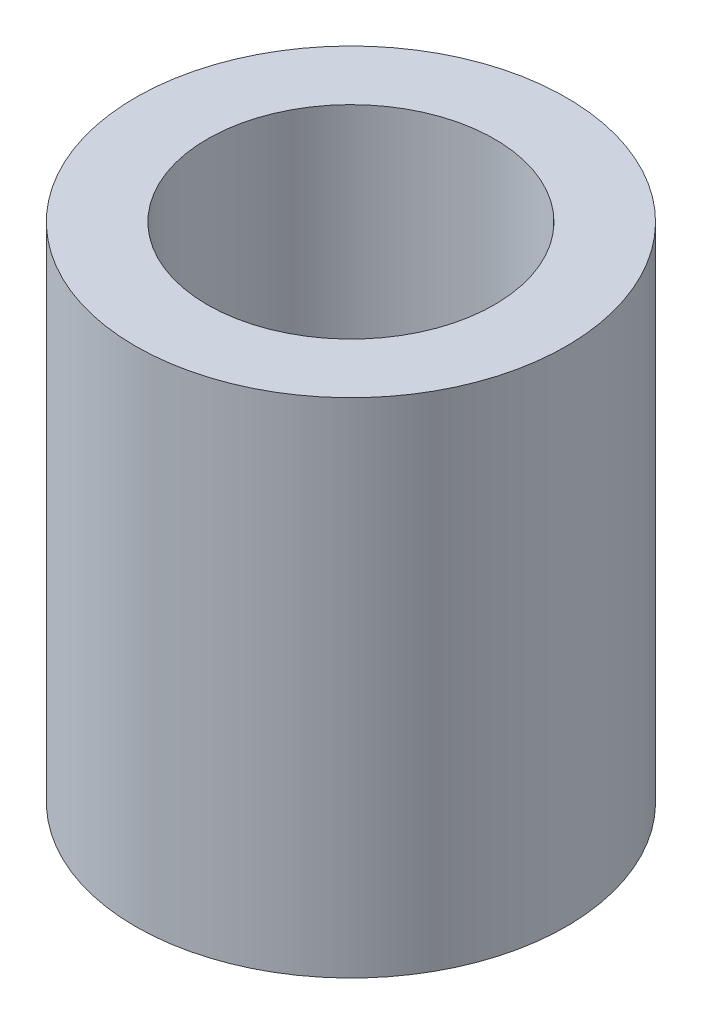
SolidWorks part; units mm, degrees
material "Латунь"
ref_plane "Спереди" through (0, 0, 0) normal (0, 0, 1) x (1, 0, 0)
ref_plane "Сверху" through (0, 0, 0) normal (0, 1, 0) x (1, 0, 0)
ref_plane "Справа" through (0, 0, 0) normal (1, 0, 0) x (0, 0, -1)
sketch "Эскиз1" plane through (0, 0, 0) normal (0, 1, 0) x (1, 0, 0)
  circle A0 centre (0, 0) radius 3
  circle A1 centre (0, 0) radius 2
  dimension "D1" = 6
  dimension "D2" = 4
extrude "Бобышка-Вытянуть1" add sketch "Эскиз1" along normal blind 7
